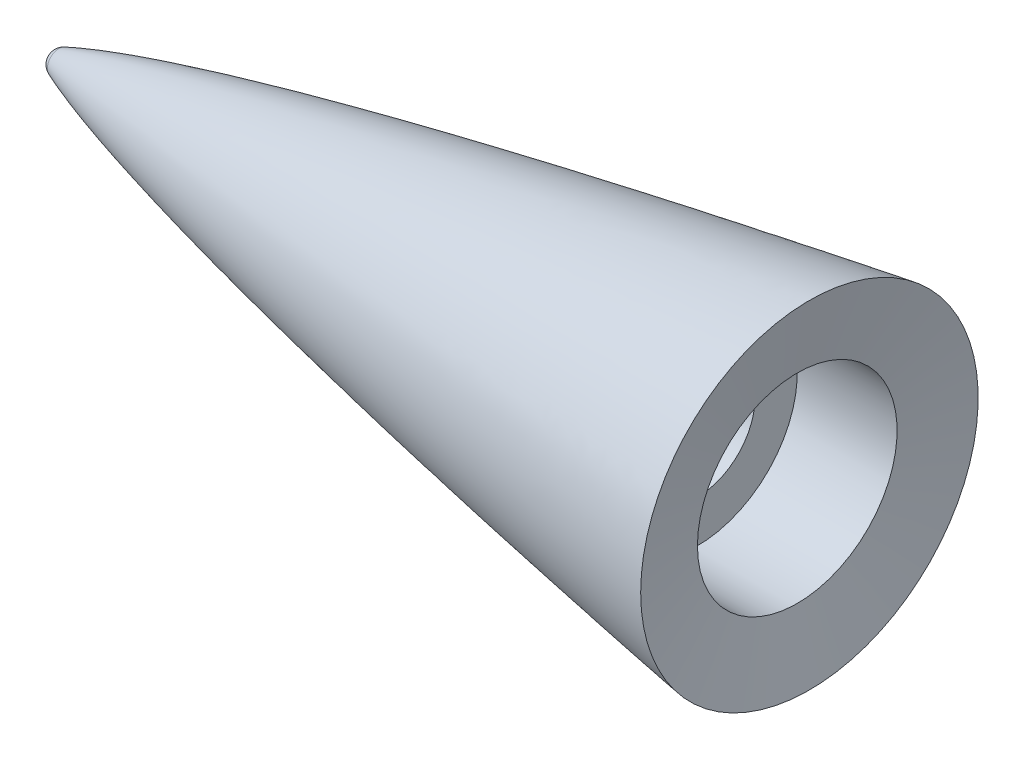
SolidWorks part; units mm, degrees
material "6061-T6 (SS)"
ref_plane "Front Plane" through (0, 0, 0) normal (0, 0, 1) x (1, 0, 0)
ref_plane "Top Plane" through (0, 0, 0) normal (0, 1, 0) x (1, 0, 0)
ref_plane "Right Plane" through (0, 0, 0) normal (1, 0, 0) x (0, 0, -1)
sketch "Sketch1" plane through (0, 0, 0) normal (0, 1, 0) x (1, 0, 0)
  line L0 (0, 0) -> (113.3431, 0) construction
  line L1 (1.6973, 0) -> (45.8194, 0)
  line L2 (83.9194, 12.7) -> (96.6194, 12.7)
  line L3 (96.6194, 12.7) -> (98.1654, 21.4679)
  line L4 (83.9194, 7.6886) -> (58.5194, 7.6886) construction
  line L5 (83.9194, 12.7) -> (82.8669, 18.9622) construction
  line L6 (58.5194, 7.6886) -> (45.8194, 0) construction
  line L7 (83.9194, 7.6886) -> (83.9194, 0)
  line L8 (83.9194, 12.7) -> (83.9194, 7.6886)
  line L9 (45.8194, 0) -> (83.9194, 0)
  arc A0 (2.6821, 1.4686) -> (1.6973, 0) centre (3.2848, 0) ccw
  spline S0 degree 4 poles (0, 0) (0.0034, 0.0099) (0.0124, 0.0287) (0.036, 0.0594) (0.0734, 0.1004) (0.1241, 0.1478) (0.1961, 0.208) (0.3018, 0.2875) (0.4718, 0.4021) (0.7529, 0.5714) (1.2295, 0.826) (2.0659, 1.2203) (3.5324, 1.8251) (5.9654, 2.7008) (9.9595, 3.9615) (15.3529, 5.459) (21.8477, 7.0868) (29.0559, 8.7493) (36.2876, 10.3139) (43.5327, 11.8013) (50.7947, 13.2272) (58.0593, 14.5995) (64.4352, 15.7629) (69.8852, 16.7323) (74.4605, 17.5301) (78.0669, 18.1509) (81.7865, 18.7815) (85.3087, 19.3727) (89.1704, 20.0106) (92.4601, 20.5499) (97.1008, 21.2989) (100.2743, 21.8052) (104.805, 22.5216) (106.4979, 22.7829) (108.0668, 23.0282) knots 0 0 0 0 0 0.000378 0.000756 0.001385 0.00201 0.00288 0.004147 0.006163 0.009417 0.014733 0.02367 0.039565 0.066726 0.108156 0.174994 0.241832 0.30867 0.375509 0.442347 0.509185 0.576023 0.642862 0.676281 0.7097 0.743119 0.776538 0.809957 0.843376 0.876795 0.910214 0.955107 1 1 1 1 1 construction
  spline S1 degree 4 poles (2.6821, 1.4686) (2.9821, 1.5917) (3.9828, 1.987) (6.0755, 2.7356) (9.9593, 3.9614) (15.3526, 5.4589) (21.8473, 7.0867) (29.0554, 8.7492) (36.2869, 10.3137) (43.5319, 11.8011) (50.7938, 13.227) (58.0582, 14.5993) (64.434, 15.7626) (69.8839, 16.7321) (74.4591, 17.5298) (78.0654, 18.1507) (81.785, 18.7813) (85.3071, 19.3724) (89.1687, 20.0104) (92.4584, 20.5496) (95.6643, 21.067) (97.3334, 21.3349) (98.165, 21.4679) (98.1654, 21.4679) knots 0.027847 0.027847 0.027847 0.027847 0.027847 0.039565 0.066726 0.108156 0.174994 0.241832 0.30867 0.375509 0.442347 0.509185 0.576023 0.642862 0.676281 0.7097 0.743119 0.776538 0.809957 0.843376 0.876795 0.910214 0.910233 0.910233 0.910233 0.910233 0.910233
  dimension "D5" = 7.6886
  dimension "D8" = 100
  dimension "D3" = 12.7
  dimension "D10" = 1.5875
  dimension "D2" = 12.7
  dimension "D4" = 25.4
  dimension "D6" = 12.7
  dimension "D7" = 6.35
revolve "Revolve2" add sketch "Sketch1" angle 360 about L0
hole_wizard "Tapped Hole for 9/16-12 Helicoil1" positions "Sketch2" profile "Sketch3" tap size "9/16-12" standard "Helicoil® Inch"
sketch "Sketch2" plane through (83.9194, 0, 0) normal (1, 0, 0) x (0, 0, -1)
  point P0 (0, 0)
cosmetic thread "Hole Thread1" parameters "D1"=25.4, "D2"=17.1475
sketch "Sketch3" plane through (83.9194, 0, 0) normal (0, 1, 0) x (0, 0, -1)
  line L0 (0, 0) -> (0, 32.3514)
  line L1 (0, 32.3514) -> (7.3419, 27.94)
  line L2 (7.3419, 27.94) -> (7.3419, 0)
  line L5 (7.3419, 0) -> (0, 0)
  line L10 (0, 32.3514) -> (-7.3419, 27.94) construction
  line L11 (0, -6.35) -> (0, 107.95) construction
  dimension "Tap Drill Dia." = 14.6837
  dimension "Tap Drill Depth" = 27.94
  dimension "Drill Angle" = 118
